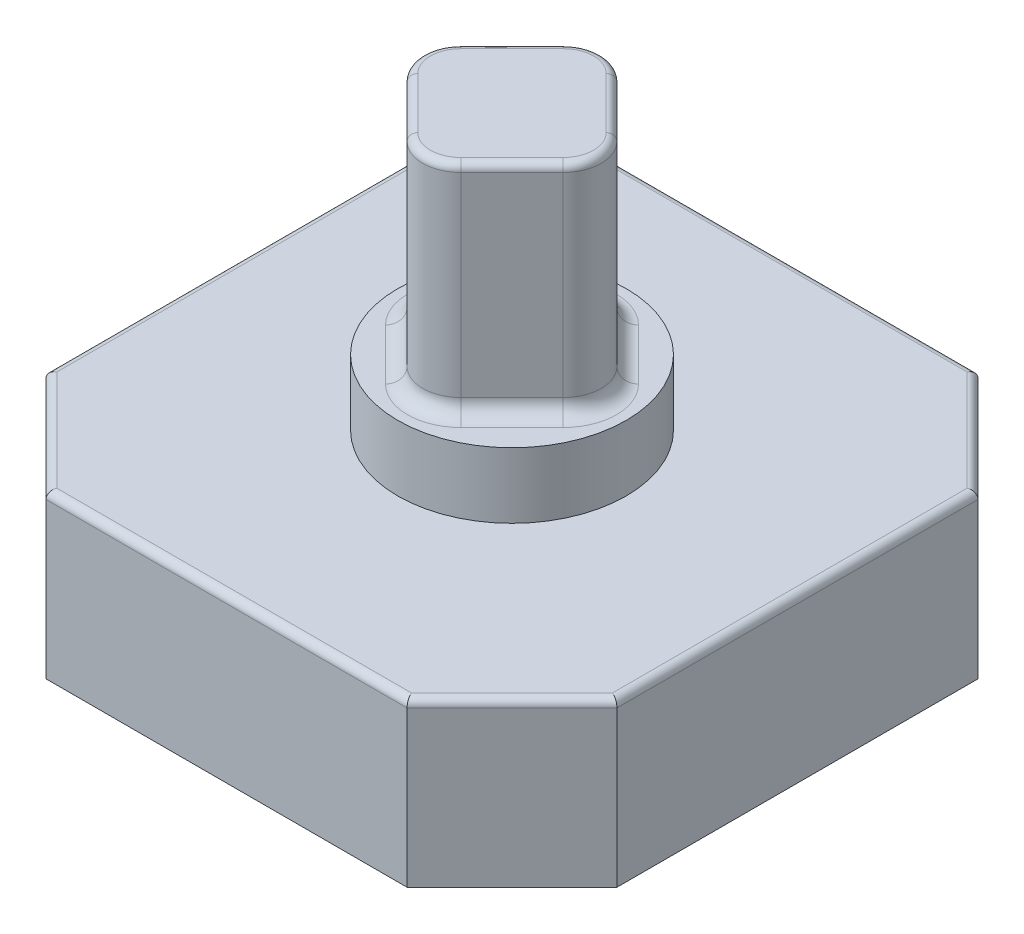
SolidWorks part; units mm, degrees
ref_plane "Front Plane" through (0, 0, 0) normal (0, 0, 1) x (1, 0, 0)
ref_plane "Top Plane" through (0, 0, 0) normal (0, 1, 0) x (1, 0, 0)
ref_plane "Right Plane" through (0, 0, 0) normal (1, 0, 0) x (0, 0, -1)
sketch "Sketch1" plane through (0, 0, 0) normal (0, 1, 0) x (1, 0, 0)
  line L0 (2.3711, -3.75) -> (3.75, -2.3711)
  line L1 (-2.3711, -3.75) -> (2.3711, -3.75)
  line L2 (-3.75, -2.3711) -> (-3.75, 2.3711)
  line L3 (-2.3711, 3.75) -> (2.3711, 3.75)
  line L4 (3.75, -2.3711) -> (3.75, 2.3711)
  line L5 (-3.0606, -3.0606) -> (3.0606, 3.0606) construction
  line L6 (-3.0606, 3.0606) -> (3.0606, -3.0606) construction
  line L7 (-3.75, 2.3711) -> (-2.3711, 3.75)
  line L8 (2.3711, 3.75) -> (3.75, 2.3711)
  line L9 (-3.75, -2.3711) -> (-2.3711, -3.75)
  point P0 (0, 0)
  dimension "D1" = 4.7423
  dimension "D2" = 4.7423
  dimension "D3" = 1.95
  dimension "D4" = 45
  dimension "D5" = 3.75
  dimension "D6" = 3.75
extrude "Boss-Extrude1" add sketch "Sketch1" along normal blind 2.14
fillet "Fillet1" radius 0.1 8 edges at (-3.0606, 2.14, 3.0606) (-3.75, 2.14, 0) (-3.0606, 2.14, -3.0606) (0, 2.14, -3.75) (3.0606, 2.14, -3.0606) (3.75, 2.14, 0) (3.0606, 2.14, 3.0606) (0, 2.14, 3.75)
sketch "Sketch2" plane through (0, 2.14, 0) normal (0, 1, 0) x (1, 0, 0)
  circle A0 centre (0, 0) radius 1.5
  dimension "D1" = 3
extrude "Boss-Extrude2" add sketch "Sketch2" along normal blind 0.86
sketch "Sketch3" plane through (0, 3, 0) normal (0, 1, 0) x (1, 0, 0)
  line L0 (-0.3536, 1.0253) -> (-1.0253, 0.3536)
  line L1 (-1.0253, -0.3536) -> (-0.3536, -1.0253)
  line L2 (0.3536, -1.0253) -> (1.0253, -0.3536)
  line L3 (1.0253, 0.3536) -> (0.3536, 1.0253)
  line L4 (-1.3789, 0) -> (1.3789, 0) construction
  arc A0 (-1.0253, 0.3536) -> (-1.0253, -0.3536) centre (-0.6718, 0) ccw
  arc A1 (-0.3536, -1.0253) -> (0.3536, -1.0253) centre (0, -0.6718) ccw
  arc A2 (1.0253, -0.3536) -> (1.0253, 0.3536) centre (0.6718, 0) ccw
  arc A3 (-0.3536, 1.0253) -> (0.3536, 1.0253) centre (0, 0.6718) cw
  point P2 (0, 0)
  point P5 (-1.6437, 0)
  point P7 (0, 0)
  point P8 (0, 0)
  point P9 (1.1328, 0.0223)
  point P15 (0, -1.3789)
  dimension "D1" = 45
  dimension "D3" = 0.5
  dimension "D2" = 1.95
extrude "Boss-Extrude3" add sketch "Sketch3" along normal blind 2.86
fillet "Fillet2" radius 0.1 8 edges at (-0.6894, 5.86, -0.6894) (0, 5.86, -1.1718) (0.6894, 5.86, -0.6894) (1.1718, 5.86, 0) (0.6894, 5.86, 0.6894) (0, 5.86, 1.1718) (-0.6894, 5.86, 0.6894) (-1.1718, 5.86, 0)
fillet "Fillet3" radius 0.2 8 edges at (-1.1718, 3, 0) (-0.6894, 3, -0.6894) (0, 3, -1.1718) (0.6894, 3, -0.6894) (1.1718, 3, 0) (0.6894, 3, 0.6894) (0, 3, 1.1718) (-0.6894, 3, 0.6894)
